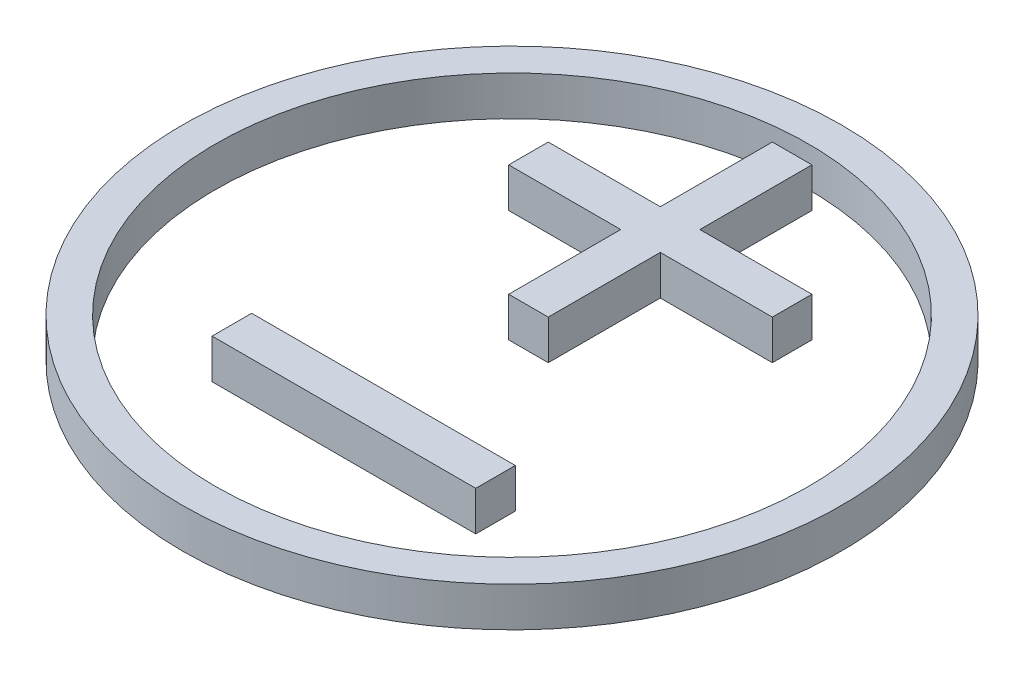
SolidWorks part; units mm, degrees
ref_plane "Front" through (0, 0, 0) normal (0, 0, 1) x (1, 0, 0)
ref_plane "Top" through (0, 0, 0) normal (0, 1, 0) x (1, 0, 0)
ref_plane "Right" through (0, 0, 0) normal (1, 0, 0) x (0, 0, -1)
sketch "Sketch1" plane through (0, 0, 0) normal (0, 1, 0) x (1, 0, 0)
  line L0 (0, 0) -> (0, 45) construction
  line L1 (0, 45) -> (0, 22.5) construction
  line L2 (0, 0) -> (0, -45) construction
  line L3 (0, -45) -> (0, -22.5) construction
  line L4 (0, -22.5) -> (0, -33.75) construction
  line L5 (0, -33.75) -> (0, 22.5)
  line L6 (0, -22.5) -> (20, -22.5) construction
  line L7 (0, -22.5) -> (-20, -22.5) construction
  line L8 (0, -19.5) -> (20, -19.5)
  line L9 (0, -19.5) -> (-20, -19.5)
  line L10 (0, -25.5) -> (20, -25.5)
  line L11 (0, -25.5) -> (-20, -25.5)
  line L12 (0, 0) -> (17.558, 0) construction
  line L13 (-20, -19.5) -> (-20, -25.5)
  line L14 (20, -25.5) -> (20, -19.5)
  line L15 (20, 25.5) -> (20, 19.5)
  line L16 (0, 25.5) -> (20, 25.5)
  line L17 (0, 25.5) -> (-20, 25.5)
  line L18 (-20, 19.5) -> (-20, 25.5)
  line L19 (0, 19.5) -> (-20, 19.5)
  line L20 (0, 19.5) -> (20, 19.5)
  line L21 (0, 22.5) -> (28.7165, -6.2165) construction
  line L22 (-3, 2.5) -> (3, 2.5)
  line L23 (3, 22.5) -> (3, 2.5)
  line L24 (3, 22.5) -> (3, 42.5)
  line L25 (3, 42.5) -> (-3, 42.5)
  line L26 (-3, 22.5) -> (-3, 42.5)
  line L27 (-3, 22.5) -> (-3, 2.5)
  circle A0 centre (0, 0) radius 50
  circle A1 centre (0, 0) radius 45
  dimension "D1" = 100
  dimension "D2" = 90
  dimension "D3" = 20
  dimension "D4" = 20
  dimension "D5" = 3
  dimension "D6" = 3
extrude "Boss-Extrude2" add sketch "Sketch1" along normal blind 6
